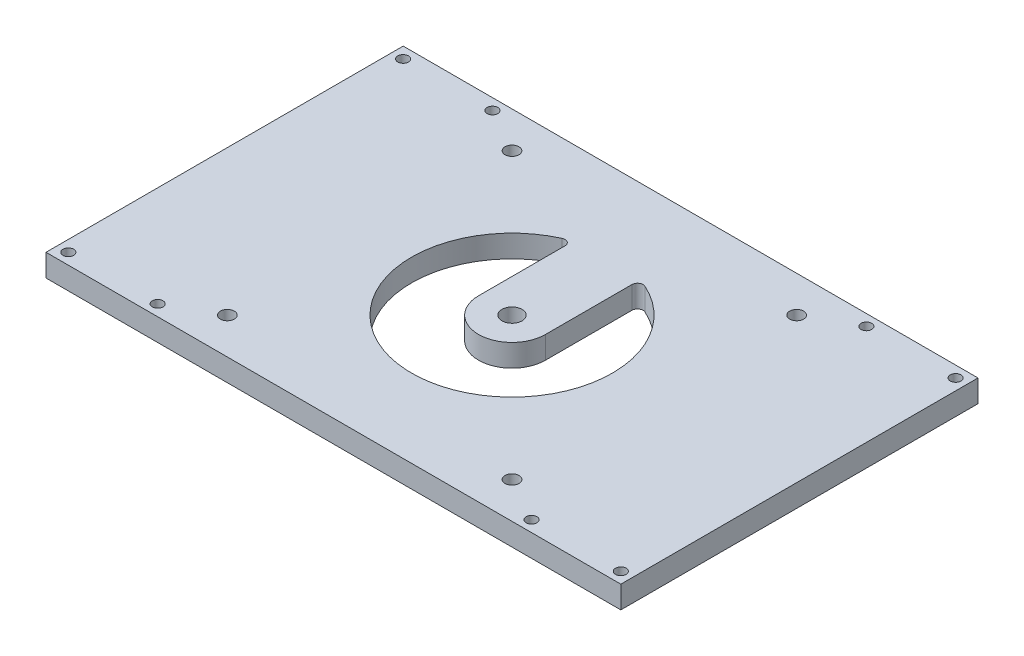
SolidWorks part; units mm, degrees
material "6061 Alloy"
ref_plane "Front Plane" through (0, 0, 0) normal (0, 0, 1) x (1, 0, 0)
ref_plane "Top Plane" through (0, 0, 0) normal (0, 1, 0) x (1, 0, 0)
ref_plane "Right Plane" through (0, 0, 0) normal (1, 0, 0) x (0, 0, -1)
sketch "Sketch2" plane through (0, 0, 0) normal (0, 1, 0) x (1, 0, 0)
  line L1 (-33.6068, 20.925) -> (129.9057, 20.925)
  line L2 (-33.6068, 20.925) -> (-33.6068, -80.675)
  line L3 (-33.6068, -80.675) -> (129.9057, -80.675)
  line L4 (129.9057, 20.925) -> (129.9057, -80.675)
  dimension "D1" = 163.5125
  dimension "D2" = 101.6
extrude "Extrude1" add sketch "Sketch2" along normal blind 6.35
sketch "Sketch3" plane through (0, 6.35, 0) normal (0, 1, 0) x (1, 0, 0)
  line L0 (-33.6068, 20.925) -> (-33.6068, -80.675) construction
  line L1 (129.9057, -80.675) -> (129.9057, 20.925) construction
  line L2 (129.9057, 20.925) -> (-33.6068, 20.925) construction
  circle A0 centre (-30.4318, 17.75) radius 1.524
  circle A1 centre (-30.4318, -77.5) radius 1.524
  circle A2 centre (126.7307, -77.5) radius 1.524
  circle A3 centre (126.7307, 17.75) radius 1.524
  circle A6 centre (-5.0318, 17.75) radius 1.524
  circle A7 centre (-5.0318, -77.5) radius 1.524
  circle A8 centre (101.3307, 17.75) radius 1.524
  circle A9 centre (101.3307, -77.5) radius 1.524
  dimension "D2" = 3.048
  dimension "D1" = 95.25
  dimension "D3" = 3.175
  dimension "D4" = 3.175
  dimension "D5" = 3.175
  dimension "D6" = 25.4
  dimension "D7" = 25.4
extrude "Cut-Extrude1" cut sketch "Sketch3" against normal through all
sketch "Sketch4" plane through (0, 6.35, 0) normal (0, 1, 0) x (1, 0, 0)
  line L0 (129.9057, 20.925) -> (-33.6068, 20.925) construction
  line L1 (-33.6068, -80.675) -> (129.9057, -80.675) construction
  line L4 (7.6618, 10.6126) -> (-33.6068, 10.6126)
  line L5 (-33.6068, 20.925) -> (-33.6068, -80.675) construction
  line L6 (88.637, 10.6126) -> (129.9057, 10.6126)
  line L7 (129.9057, -80.675) -> (129.9057, 20.925) construction
  circle A0 centre (7.6618, 10.6126) radius 1.9844
  circle A1 centre (88.637, 10.6126) radius 1.9844
  circle A2 centre (7.6618, -70.3626) radius 1.9844
  circle A3 centre (88.637, -70.3626) radius 1.9844
  point P12 (-74.0556, -33.8042)
  dimension "D4" = 3.9688
  dimension "D1" = 10.3124
  dimension "D2" = 80.9752
  dimension "D3" = 10.3124
extrude "Cut-Extrude2" cut sketch "Sketch4" against normal through all
sketch "Sketch5" plane through (0, 6.35, 0) normal (0, 1, 0) x (1, 0, 0)
  line L1 (-33.6068, 20.925) -> (-33.6068, -80.675) construction
  circle A0 centre (48.1494, -29.875) radius 2.85
  point P2 (48.1494, 0.7851)
  point P3 (-33.6068, -29.875)
  dimension "D1" = 5.7
extrude "Cut-Extrude3" cut sketch "Sketch5" against normal through all
sketch "Sketch6" plane through (0, 0, 0) normal (0, -1, 0) x (1, 0, 0)
  line L0 (38.6244, 29.875) -> (38.6244, 5.2816)
  line L1 (57.6744, 29.875) -> (57.6744, 5.2816)
  line L2 (-33.6068, -20.925) -> (-33.6068, 80.675) construction
  circle A0 centre (48.1494, 29.875) radius 28.575
  arc A1 (57.6744, 29.875) -> (38.6244, 29.875) centre (48.1494, 29.875) ccw
  arc A2 (36.3833, 3.8349) -> (38.6244, 5.2816) centre (37.0369, 5.2816) ccw
  arc A3 (57.6744, 5.2816) -> (59.9156, 3.8349) centre (59.2619, 5.2816) ccw
  dimension "D1" = 57.15
  dimension "D2" = 19.05
  dimension "D3" = 3.175
extrude "Cut-Extrude4" cut sketch "Sketch6" against normal through all
